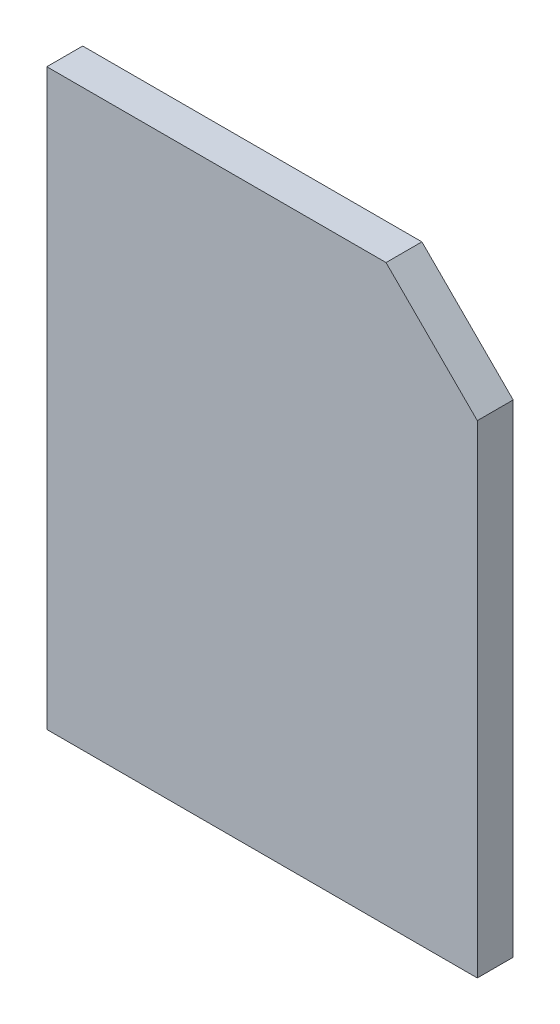
SolidWorks part; units mm, degrees
ref_plane "前视基准面" through (0, 0, 0) normal (0, 0, 1) x (1, 0, 0)
ref_plane "上视基准面" through (0, 0, 0) normal (0, 1, 0) x (1, 0, 0)
ref_plane "右视基准面" through (0, 0, 0) normal (1, 0, 0) x (0, 0, -1)
other "Configuration Table"
sketch "草图1" plane through (0, 0, 0) normal (0, 0, 1) x (1, 0, 0)
  line L1 (12, -16) -> (-12, -16)
  line L2 (12, -16) -> (12, 16)
  line L3 (12, 16) -> (-12, 16)
  line L4 (-12, -16) -> (-12, 16)
  line L5 (12, -16) -> (-12, 16) construction
  line L6 (12, 16) -> (-12, -16) construction
  point P0 (0, 0)
extrude "凸台-拉伸1" add sketch "草图1" along normal blind 2
sketch "草图2" plane through (0, 0, 2) normal (0, 0, 1) x (1, 0, 0)
  line L0 (6.9117, 16) -> (12, 10.9117)
  line L1 (12, 16) -> (-12, 16) construction
  line L2 (12, -16) -> (12, 16) construction
  line L7 (-12, 16) -> (-12, -16)
  line L8 (-12, -16) -> (12, -16)
  line L9 (12, -16) -> (12, 16)
  line L10 (12, 16) -> (-12, 16)
  line L13 (12, 10.9117) -> (12, 16)
  line L14 (12, 16) -> (6.9117, 16)
  point P6 (-12, -16)
  dimension "D1" = 36
  dimension "D2" = 0
extrude "切除-拉伸1" cut sketch "草图2" against normal blind 2 contours L13 L14 L0
